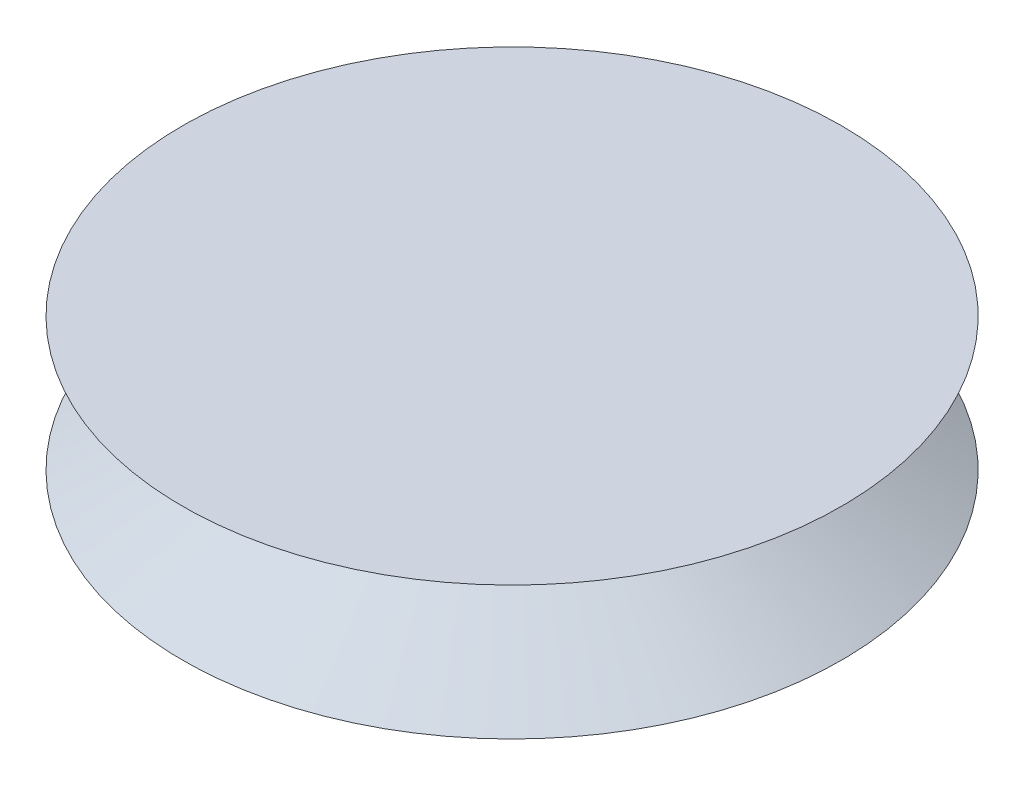
SolidWorks part; units mm, degrees
ref_plane "Front Plane" through (0, 0, 0) normal (0, 0, 1) x (1, 0, 0)
ref_plane "Top Plane" through (0, 0, 0) normal (0, 1, 0) x (1, 0, 0)
ref_plane "Right Plane" through (0, 0, 0) normal (1, 0, 0) x (0, 0, -1)
sketch "Sketch3" plane through (0, 0, 0) normal (0, 0, 1) x (1, 0, 0)
  line L0 (-131.4239, 48.6742) -> (-68.9358, 48.6742)
  line L1 (-68.9358, 48.6742) -> (-68.9358, 73.9481)
  line L2 (-68.9358, 73.9481) -> (-131.4239, 73.9481)
  line L3 (-131.4239, 73.9481) -> (-107.1451, 63.2017)
  line L4 (-107.1451, 63.2017) -> (-131.4239, 48.6742)
  point P2 (-123.6627, 55.938)
revolve "Revolve4" add sketch "Sketch3" angle 360 about L1
